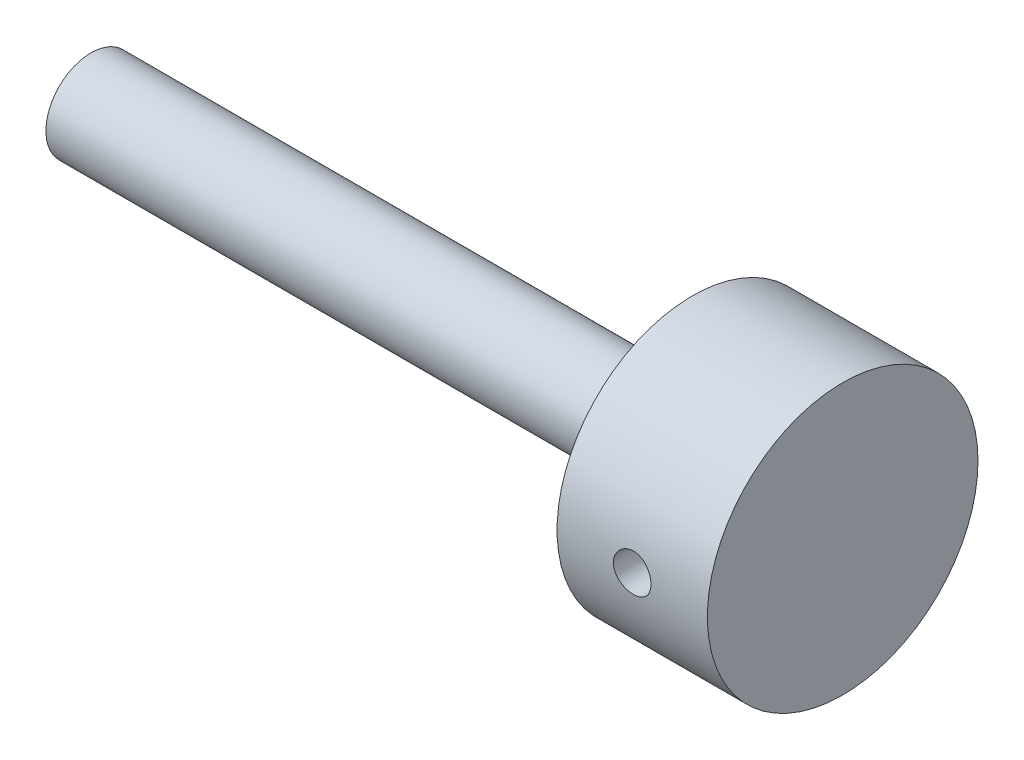
SolidWorks part; units mm, degrees
ref_plane "Ön Düzlem" through (0, 0, 0) normal (0, 0, 1) x (1, 0, 0)
ref_plane "Üst Düzlem" through (0, 0, 0) normal (0, 1, 0) x (1, 0, 0)
ref_plane "Sağ Düzlem" through (0, 0, 0) normal (1, 0, 0) x (0, 0, -1)
sketch "Çizim1" plane through (0, 0, 0) normal (0, 0, 1) x (1, 0, 0)
  line L0 (-20.2352, 0) -> (59.7648, 0)
  line L1 (59.7648, 0) -> (59.7648, -12)
  line L2 (59.7648, -12) -> (79.7648, -12)
  line L3 (79.7648, -12) -> (79.7648, 0.2415)
  line L4 (79.7648, 0.2415) -> (79.7648, 6)
  line L5 (79.7648, 6) -> (-20.2352, 6)
  line L6 (-20.2352, 6) -> (-20.2352, 0)
  dimension "D1" = 100
  dimension "D2" = 20
  dimension "D3" = 12
  dimension "D4" = 6
revolve "Döndür1" add sketch "Çizim1" angle 360 about L5
ref_plane "Düzlem1" through (69.76, 0, 0) normal (1, 0, 0) x (0, 0, -1)
ref_plane "Düzlem2" through (0, 6, 0) normal (0, 1, 0) x (1, 0, 0)
sketch "Çizim2" plane through (0, 0, 0) normal (0, 0, 1) x (1, 0, 0)
  line L0 (19.8, 6) -> (-19.8, 6) construction
  line L1 (69.76, -19.8) -> (69.76, 19.8) construction
  circle A0 centre (69.76, 6) radius 2.5
  point P6 (0, 0)
  dimension "D1" = 5
extrude "Kes-Ekstrüzyon1" cut sketch "Çizim2" against normal mid plane 105
